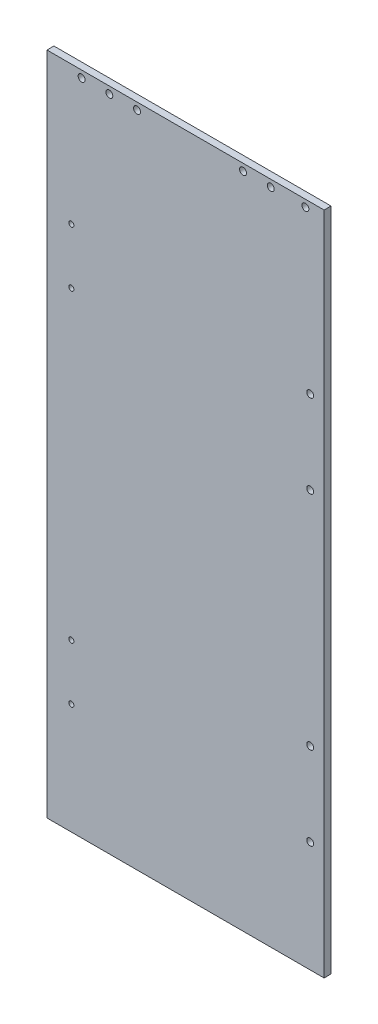
SolidWorks part; units mm, degrees
material "PC High Viscosity"
ref_plane "Front Plane" through (0, 0, 0) normal (0, 0, 1) x (1, 0, 0)
ref_plane "Top Plane" through (0, 0, 0) normal (0, 1, 0) x (1, 0, 0)
ref_plane "Right Plane" through (0, 0, 0) normal (1, 0, 0) x (0, 0, -1)
sketch "Sketch1" plane through (0, 0, 0) normal (0, 0, 1) x (1, 0, 0)
  line L1 (-28.575, 0) -> (225.425, 0)
  line L2 (-28.575, 0) -> (-28.575, -609.6)
  line L3 (-28.575, -609.6) -> (225.425, -609.6)
  line L4 (225.425, 0) -> (225.425, -609.6)
  dimension "D1" = 254
  dimension "D2" = 609.6
  dimension "D3" = 225.425
extrude "Boss-Extrude1" add sketch "Sketch1" along normal blind 6.35
sketch "Sketch2" plane through (0, 0, 6.35) normal (0, 0, 1) x (1, 0, 0)
  line L0 (-28.575, 0) -> (-28.575, -609.6) construction
  line L1 (-28.575, -609.6) -> (225.425, -609.6) construction
  circle A0 centre (-6.223, -127) radius 2.3812
  circle A1 centre (-6.223, -177.8) radius 2.3812
  circle A2 centre (-6.223, -457.2) radius 2.3813
  circle A3 centre (-6.223, -508) radius 2.3813
  dimension "D5" = 4.7625
  dimension "D1" = 22.352
  dimension "D2" = 50.8
  dimension "D3" = 279.4
  dimension "D4" = 50.8
  dimension "D6" = 101.6
extrude "Cut-Extrude1" cut sketch "Sketch2" against normal through all
sketch "Sketch3" plane through (0, 0, 0) normal (0, 0, -1) x (-1, 0, 0)
  line L0 (-225.425, 0) -> (28.575, 0) construction
  line L2 (28.575, 0) -> (28.575, -609.6) construction
  line L3 (-225.425, -609.6) -> (-225.425, 0) construction
  circle A0 centre (-208.28, -6.35) radius 3.175
  circle A1 centre (-176.53, -6.35) radius 3.175
  circle A2 centre (-151.13, -6.35) radius 3.175
  circle A3 centre (-53.975, -6.35) radius 3.175
  circle A4 centre (-28.575, -6.35) radius 3.175
  circle A5 centre (-3.175, -6.35) radius 3.175
  dimension "D4" = 6.35
  dimension "D1" = 31.75
  dimension "D2" = 25.4
  dimension "D3" = 6.35
  dimension "D5" = 17.145
  dimension "D6" = 31.75
  dimension "D7" = 25.4
  dimension "D8" = 25.4
extrude "Cut-Extrude2" cut sketch "Sketch3" against normal through all
sketch "Sketch4" plane through (0, 0, 6.35) normal (0, 0, 1) x (1, 0, 0)
  line L0 (-28.575, -609.6) -> (225.425, -609.6) construction
  line L1 (225.425, -609.6) -> (225.425, 0) construction
  line L2 (225.425, 0) -> (-28.575, 0) construction
  circle A0 centre (212.7067, -431.8) radius 3.175
  circle A1 centre (212.7067, -508) radius 3.175
  circle A2 centre (212.7067, -228.6) radius 3.175
  circle A3 centre (212.7067, -152.4) radius 3.175
  dimension "D3" = 6.35
  dimension "D5" = 6.35
  dimension "D1" = 76.2
  dimension "D2" = 101.6
  dimension "D4" = 12.7183
  dimension "D6" = 76.2
  dimension "D7" = 152.4
extrude "Cut-Extrude3" cut sketch "Sketch4" against normal through all
